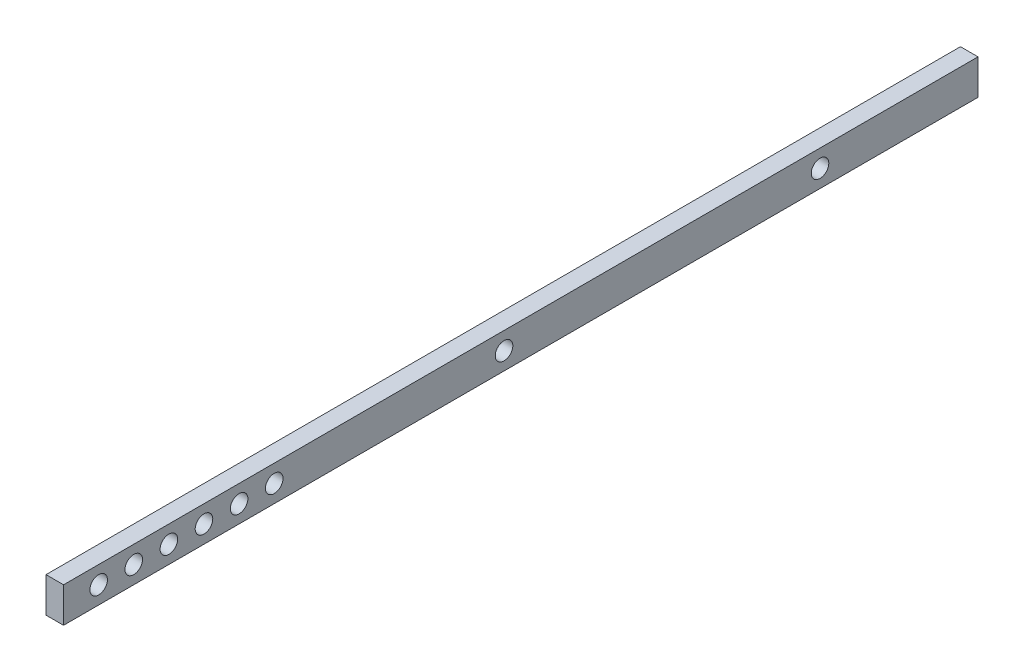
SolidWorks part; units mm, degrees
ref_plane "Front Plane" through (0, 0, 0) normal (0, 0, 1) x (1, 0, 0)
ref_plane "Top Plane" through (0, 0, 0) normal (0, 1, 0) x (1, 0, 0)
ref_plane "Right Plane" through (0, 0, 0) normal (1, 0, 0) x (0, 0, -1)
sketch "Sketch1" plane through (0, 0, 0) normal (1, 0, 0) x (0, 0, -1)
  line L0 (6.35, 6.35) -> (6.35, 0) construction
  line L5 (0, 0) -> (63.5, 0)
  line L6 (0, 0) -> (0, 6.35)
  line L7 (0, 6.35) -> (63.5, 6.35)
  line L8 (63.5, 0) -> (63.5, 6.35)
  line L9 (57.15, 6.35) -> (57.15, 0) construction
  line L10 (57.15, 6.35) -> (63.5, 0) construction
  line L11 (6.35, 6.35) -> (0, 0) construction
  line L12 (-76.495, 3.175) -> (0, 3.175) construction
  line L13 (0, 6.35) -> (-76.495, 6.35)
  line L14 (0, 6.35) -> (0, 0)
  line L15 (0, 0) -> (-76.495, 0)
  line L16 (-76.495, 6.35) -> (-76.495, 0)
  line L18 (63.5, 6.35) -> (88.9, 6.35)
  line L19 (63.5, 6.35) -> (63.5, 0)
  line L20 (63.5, 0) -> (88.9, 0)
  line L21 (88.9, 6.35) -> (88.9, 0)
  circle A0 centre (60.325, 3.175) radius 1.5875
  circle A1 centre (3.175, 3.175) radius 1.5875
  circle A2 centre (-38.395, 3.175) radius 1.5875
  circle A4 centre (-44.745, 3.175) radius 1.5875
  circle A5 centre (-51.095, 3.175) radius 1.5875
  circle A6 centre (-57.445, 3.175) radius 1.5875
  circle A7 centre (-63.795, 3.175) radius 1.5875
  circle A8 centre (-70.145, 3.175) radius 1.5875
  point P5 (60.325, 3.175)
  point P12 (3.175, 3.175)
  dimension "D3" = 3.175
  dimension "D4" = 3.175
  dimension "D8" = 3.175
  dimension "D1" = 63.5
  dimension "D2" = 6.35
  dimension "D5" = 6.35
  dimension "D6" = 6.35
  dimension "D7" = 41.57
  dimension "D9" = 6
  dimension "D10" = 6.35
  dimension "D11" = 6.35
  dimension "D12" = 25.4
extrude "Boss-Extrude1" add sketch "Sketch1" along normal blind 3.175 contours L13 L16 L15 L6 A8 A7 A6 A5 A4 A2 | L5 L8 L7 L6 A1 A0 | L19 L18 L21 L20
